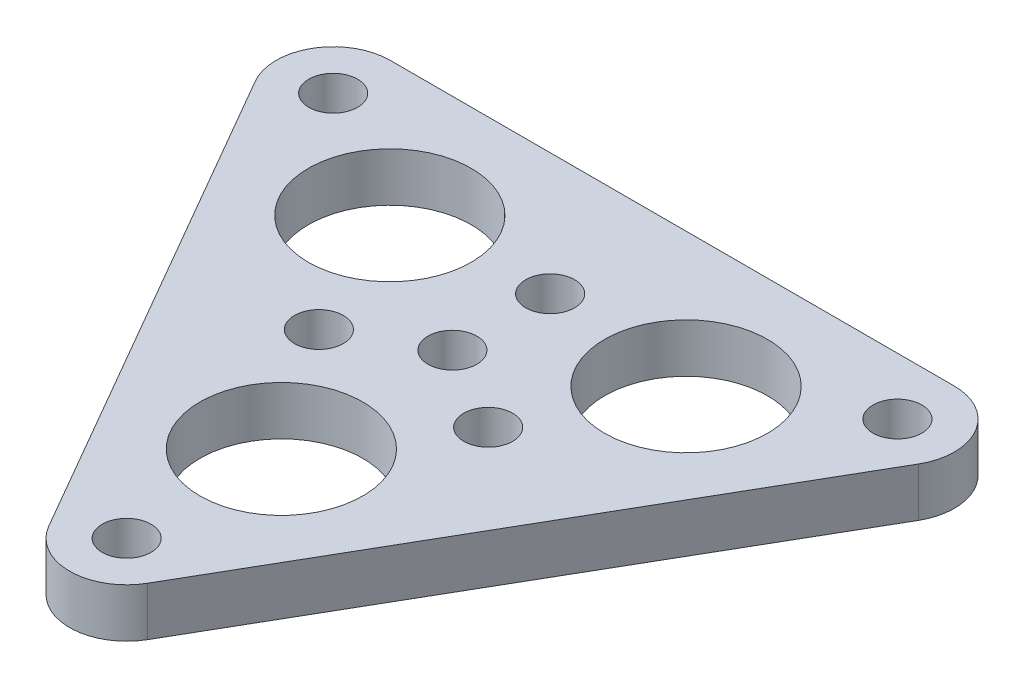
SolidWorks part; units mm, degrees
material "Thornel Mat VMA"
ref_plane "前视基准面" through (0, 0, 0) normal (0, 0, 1) x (1, 0, 0)
ref_plane "上视基准面" through (0, 0, 0) normal (0, 1, 0) x (1, 0, 0)
ref_plane "右视基准面" through (0, 0, 0) normal (1, 0, 0) x (0, 0, -1)
sketch "草图1" plane through (0, 0, 0) normal (0, 1, 0) x (-1, 0, 0)
  line L0 (0, 0) -> (0, 20) construction
  line L1 (-3.0311, 21.75) -> (-20.3516, -8.25)
  line L2 (20.3516, -8.25) -> (3.0311, 21.75)
  line L3 (-17.3205, -13.5) -> (17.3205, -13.5)
  circle A0 centre (0, 20) radius 1.5
  circle A1 centre (17.3205, -10) radius 1.5
  circle A2 centre (-17.3205, -10) radius 1.5
  circle A3 centre (0, 0) radius 20 construction
  circle A4 centre (-5.1962, 3) radius 1.5
  arc A5 (3.0311, 21.75) -> (-3.0311, 21.75) centre (0, 20) ccw
  arc A6 (17.3205, -13.5) -> (20.3516, -8.25) centre (17.3205, -10) ccw
  arc A7 (-20.3516, -8.25) -> (-17.3205, -13.5) centre (-17.3205, -10) ccw
  circle A8 centre (0, 0) radius 1.5
  circle A9 centre (0, 10.5) radius 5
  circle A10 centre (9.0933, -5.25) radius 5
  circle A11 centre (-9.0933, -5.25) radius 5
  circle A12 centre (0, 0) radius 6 construction
  circle A13 centre (0, -6) radius 1.5
  circle A14 centre (5.1962, 3) radius 1.5
  dimension "D2" = 3
  dimension "D4" = 12
  dimension "D1" = 40
  dimension "D5" = 10
  dimension "D6" = 10.5
  dimension "D7" = 3.5
  dimension "D3" = 3
extrude "凸台-拉伸1" add sketch "草图1" along normal blind 3
